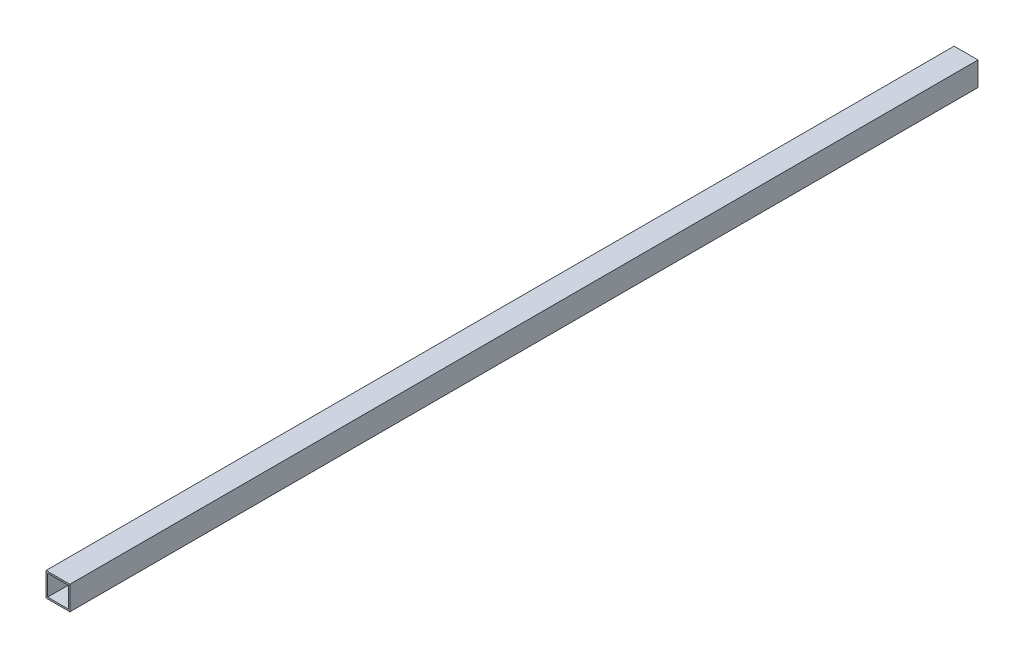
SolidWorks part; units mm, degrees
ref_plane "Front Plane" through (0, 0, 0) normal (0, 0, 1) x (1, 0, 0)
ref_plane "Top Plane" through (0, 0, 0) normal (0, 1, 0) x (1, 0, 0)
ref_plane "Right Plane" through (0, 0, 0) normal (1, 0, 0) x (0, 0, -1)
curve "Curve1"
  spline degree 1 poles (0, 0, -1140) (0, 0, 1140) knots 0 0 1 1
sketch "Sketch1" plane through (0, 0, 0) normal (0, 0, 1) x (1, 0, 0)
  line L0 (0, 35.3535) -> (0, -33.8384) construction
  line L1 (-30, 30) -> (30, 30)
  line L2 (-30, 30) -> (-30, -30)
  line L3 (-30, -30) -> (30, -30)
  line L4 (30, 30) -> (30, -30)
  line L5 (-26, 26) -> (26, 26)
  line L6 (-26, 26) -> (-26, -26)
  line L7 (-26, -26) -> (26, -26)
  line L8 (26, 26) -> (26, -26)
  line L9 (-39.3939, 0) -> (41.5152, 0) construction
  dimension "D1" = 60
  dimension "D2" = 52
sweep "Sweep1" add profiles "Sketch1" path "Curve1"
